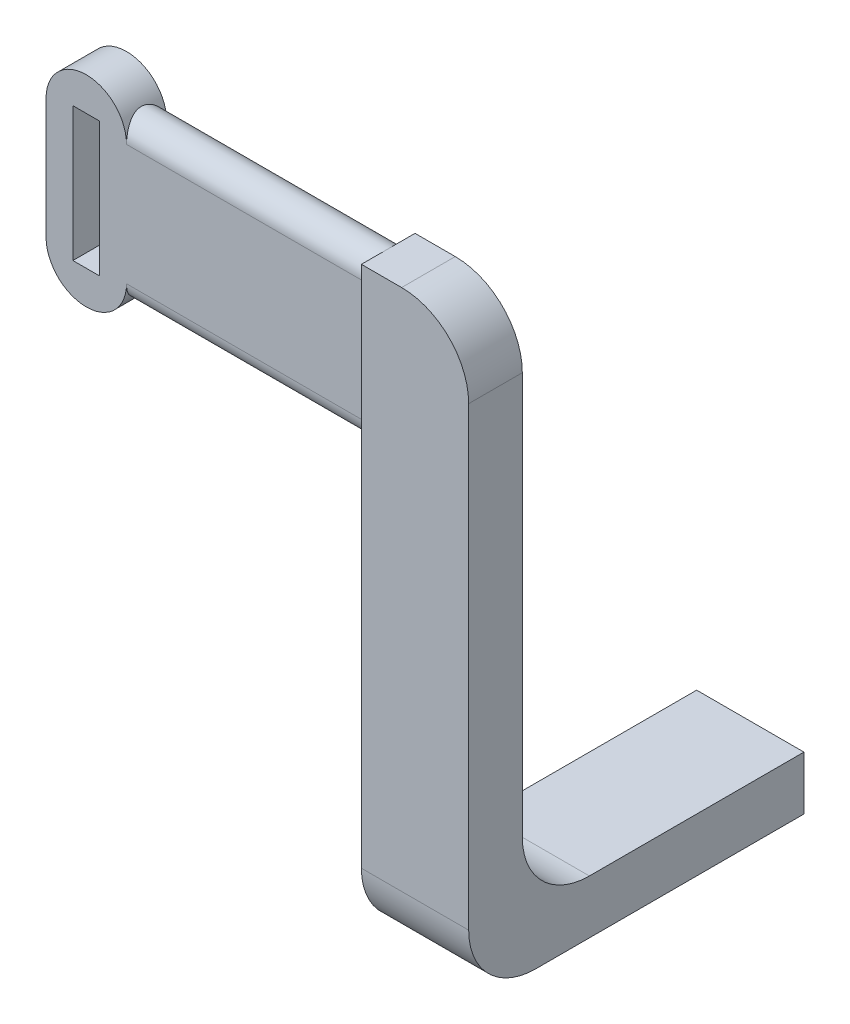
SolidWorks part; units mm, degrees
ref_plane "Front Plane" through (0, 0, 0) normal (0, 0, 1) x (1, 0, 0)
ref_plane "Top Plane" through (0, 0, 0) normal (0, 1, 0) x (1, 0, 0)
ref_plane "Right Plane" through (0, 0, 0) normal (1, 0, 0) x (0, 0, -1)
sketch "Arm Feature Sketch" plane through (0, 0, 0) normal (0, 0, 1) x (1, 0, 0)
  line L1 (-8, 4) -> (8, 4)
  line L2 (-8, 4) -> (-8, -4)
  line L3 (-8, -4) -> (8, -4)
  line L4 (8, 4) -> (8, -4)
  line L5 (-8, 4) -> (8, -4) construction
  line L6 (-8, -4) -> (8, 4) construction
  point P0 (0, 0)
  dimension "D1" = 16
  dimension "D2" = 8
extrude "Arm Feature" add sketch "Arm Feature Sketch" along normal blind 50 contours L1 L4 L3 L2
sketch "Tab Feature Sketch" plane through (0, -4, 0) normal (0, 1, 0) x (1, 0, 0)
  line L0 (-4, 0) -> (4, 0)
  line L1 (-4, 0) -> (-4, -25)
  line L2 (4, 0) -> (4, -25)
  line L3 (-4, -25) -> (4, -25)
  line L4 (-8, 0) -> (8, 0) construction
  dimension "D1" = 25
  dimension "D2" = 8
extrude "Tab Feature" cut sketch "Tab Feature Sketch" along normal blind 5
sketch "Leg Feature Sketch" plane through (0, 4, 0) normal (0, 1, 0) x (1, 0, 0)
  line L0 (-8, -50) -> (8, -50)
  line L1 (-8, -50) -> (-8, -42)
  line L2 (8, -50) -> (8, -42)
  line L3 (-8, -42) -> (8, -42)
  dimension "D1" = 8
extrude "Leg Feature" add sketch "Leg Feature Sketch" along normal blind 80
sketch "Slot Feature Sketch" plane through (-8, 0, 0) normal (1, 0, 0) x (0, 0, -1)
  line L0 (-46.0252, 81) -> (-46.0252, 63) construction
  line L1 (-43.0252, 81) -> (-43.0252, 63)
  line L2 (-49.0252, 81) -> (-49.0252, 63)
  line L3 (-50, 84) -> (-42, 84) construction
  arc A0 (-43.0252, 81) -> (-49.0252, 81) centre (-46.0252, 81) ccw
  arc A1 (-49.0252, 63) -> (-43.0252, 63) centre (-46.0252, 63) ccw
  point P2 (-46.0252, 72)
  dimension "D1" = 12
  dimension "D2" = 6
  dimension "D3" = 18
extrude "Slot Feature" add sketch "Slot Feature Sketch" against normal blind 42
sketch "Strap Feature Sketch" plane through (0, 0, 43.0252) normal (0, 0, -1) x (-1, 0, 0)
  line L0 (50, 63) -> (50, 81) construction
  line L1 (50, 63) -> (50, 81) construction
  line L2 (44, 63) -> (44, 81)
  line L3 (56, 63) -> (56, 81)
  arc A0 (44, 63) -> (56, 63) centre (50, 63) ccw
  arc A1 (56, 81) -> (44, 81) centre (50, 81) ccw
  point P5 (50, 72)
extrude "Strap Feature" add sketch "Strap Feature Sketch" against normal blind 6
sketch "Strap Cut Sketch" plane through (0, 0, 43.0252) normal (0, 0, 1) x (1, 0, 0)
  line L1 (-52, 82) -> (-48, 82)
  line L2 (-52, 82) -> (-52, 62)
  line L3 (-52, 62) -> (-48, 62)
  line L4 (-48, 82) -> (-48, 62)
  line L5 (-52, 82) -> (-48, 62) construction
  line L6 (-52, 62) -> (-48, 82) construction
  point P0 (-50, 72)
  dimension "D1" = 20
  dimension "D2" = 4
extrude "Strap Cut" cut sketch "Strap Cut Sketch" along normal blind 6 contours L2 L3 L4 L1
fillet "Fillet1" radius 10 1 edges at (0, -4, 50)
fillet "Fillet2" radius 10 1 edges at (0, 4, 42)
fillet "Fillet3" radius 10 1 edges at (8, 84, 46)
